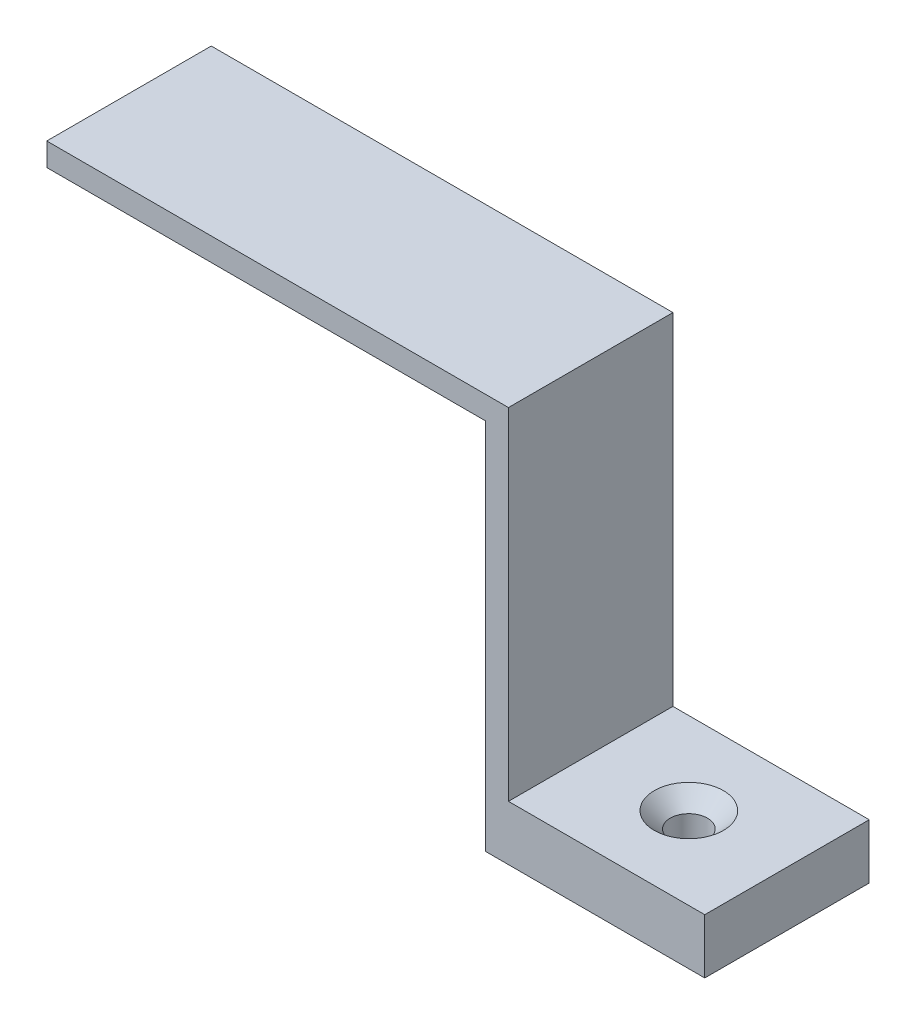
SolidWorks part; units mm, degrees
ref_plane "Alzado" through (0, 0, 0) normal (0, 0, 1) x (1, 0, 0)
ref_plane "Planta" through (0, 0, 0) normal (0, 1, 0) x (1, 0, 0)
ref_plane "Vista lateral" through (0, 0, 0) normal (1, 0, 0) x (0, 0, -1)
sketch "Croquis1" plane through (0, 0, 0) normal (0, 0, 1) x (1, 0, 0)
  line L0 (-24.2778, -18.7792) -> (-24.2778, -23.7792)
  line L1 (-24.2778, -23.7792) -> (-44.2778, -23.7792)
  line L2 (-44.2778, -23.7792) -> (-44.2778, 10.2208)
  line L3 (-44.2778, 10.2208) -> (-84.2778, 10.2208)
  line L4 (-84.2778, 10.2208) -> (-84.2778, 12.3208)
  line L5 (-84.2778, 12.3208) -> (-42.1778, 12.3208)
  line L6 (-42.1778, 12.3208) -> (-42.1778, -18.7792)
  line L7 (-42.1778, -18.7792) -> (-24.2778, -18.7792)
  dimension "D1" = 2.1
  dimension "D2" = 2.1
  dimension "D3" = 5
  dimension "D4" = 34
  dimension "D5" = 40
  dimension "D6" = 20
extrude "Saliente-Extruir1" add sketch "Croquis1" along normal blind 15
sketch "Croquis2" plane through (0, -18.7792, 0) normal (0, 1, 0) x (1, 0, 0)
  line L0 (-42.1778, 0) -> (-24.2778, -15) construction
  circle A0 centre (-33.2278, -7.5) radius 1.5
extrude "Cortar-Extruir1" cut sketch "Croquis2" against normal up to vertex (5 mm away)
hole_wizard "Avellanado para tornillo con cabeza plana avellanada de M31" positions "Croquis5" profile "Croquis6" countersink size "M3" standard "ISO" end condition through all
sketch "Croquis5" plane through (0, -18.7792, 0) normal (0, 1, 0) x (1, 0, 0)
  point P0 (-33.2278, -7.5)
sketch "Croquis6" plane through (-33.2278, -18.7792, 7.5) normal (1, 0, 0) x (0, 0, 1)
  line L0 (0, 0) -> (0, 5)
  line L1 (0, 5) -> (1.7, 5)
  line L2 (1.7, 5) -> (1.7, 1.45)
  line L3 (1.7, 1.45) -> (3.15, 0)
  line L5 (3.15, 0) -> (0, 0)
  line L6 (-1.7, 1.45) -> (-3.15, 0) construction
  line L11 (0, -6.35) -> (0, 107.95) construction
  dimension "Diámetro de taladro hasta el siguiente" = 3.4
  dimension "Profundidad de taladro hasta el siguiente" = 5
  dimension "Diámetro de avellanado cercano" = 6.3
  dimension "Ángulo de avellanado cercano" = 90
